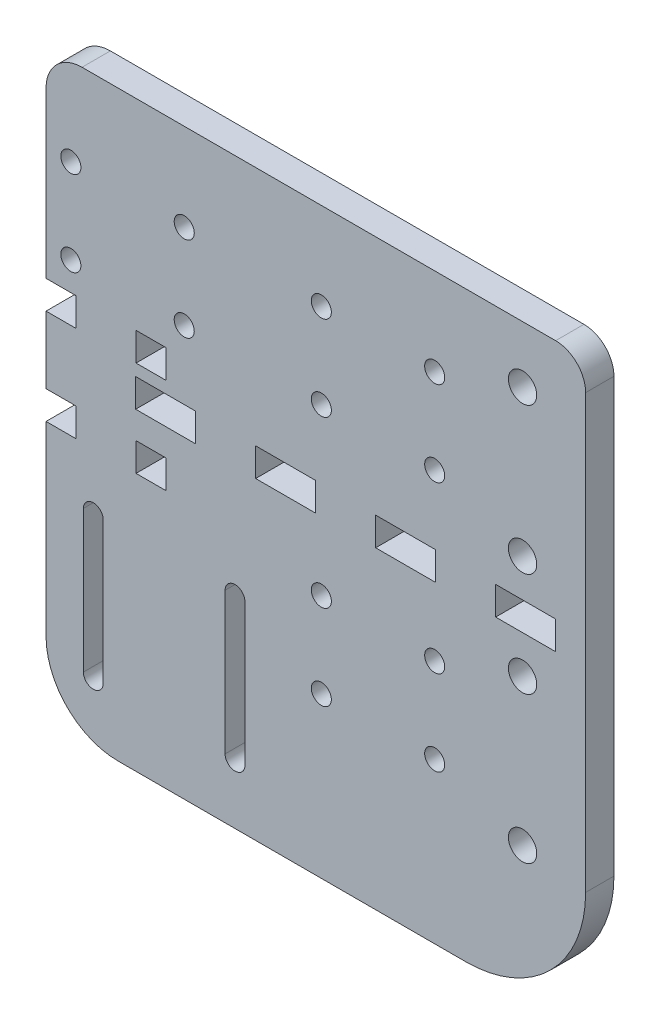
SolidWorks part; units mm, degrees
ref_plane "Front Plane" through (0, 0, 0) normal (0, 0, 1) x (1, 0, 0)
ref_plane "Top Plane" through (0, 0, 0) normal (0, 1, 0) x (1, 0, 0)
ref_plane "Right Plane" through (0, 0, 0) normal (1, 0, 0) x (0, 0, -1)
sketch "Sketch1" plane through (0, 0, 0) normal (0, 0, 1) x (-1, 0, 0)
  line L0 (72.0987, 7.3834) -> (72.0987, -6.8406)
  line L1 (32.0987, 55.3834) -> (32.0987, 25.3834) construction
  line L2 (46.6987, 13.3834) -> (53.0487, 13.3834)
  line L4 (46.6987, 13.3834) -> (46.6987, 7.3834)
  line L5 (46.6987, 7.3834) -> (53.0487, 7.3834)
  line L7 (72.0987, -42.8406) -> (72.0987, -12.8406)
  line L8 (-15.4204, 10.1785) -> (-15.4204, -12.8406)
  line L9 (-35.7704, 4.6785) -> (-35.7704, 45.6785) construction
  line L10 (-35.7704, 45.6785) -> (-21.7704, 45.6785) construction
  line L11 (-21.7704, 45.6785) -> (-21.7704, 4.6785) construction
  line L12 (-21.7704, 4.6785) -> (-35.7704, 4.6785) construction
  line L13 (-1015.4204, -1.3311) -> (48984.5796, -1.3311) construction
  line L14 (-15.4204, 25.1785) -> (-21.7704, 25.1785)
  line L15 (-21.7704, -7.3406) -> (-35.7704, -7.3406) construction
  line L16 (-21.7704, -48.3406) -> (-21.7704, -7.3406) construction
  line L17 (-35.7704, -48.3406) -> (-21.7704, -48.3406) construction
  line L18 (-35.7704, -7.3406) -> (-35.7704, -48.3406) construction
  line L19 (34.1987, 55.3834) -> (34.1987, 25.3834)
  line L20 (29.9987, 55.3834) -> (29.9987, 25.3834)
  line L21 (62.0987, 55.3834) -> (62.0987, 25.3834) construction
  line L22 (-15.4204, 40.1785) -> (-15.4204, 10.1785)
  line L23 (72.0987, -42.8406) -> (72.0987, -47.7342)
  line L24 (64.4787, -55.3542) -> (51.6526, -55.3542)
  line L25 (53.0487, 13.3834) -> (53.0487, 7.3834)
  line L26 (73.3068, 13.3834) -> (74.536, 13.3834) construction
  line L27 (65.7487, 13.3834) -> (72.0987, 13.3834)
  line L28 (65.7487, 13.3834) -> (65.7487, 7.3834)
  line L29 (65.7487, 7.3834) -> (72.0987, 7.3834)
  line L30 (64.1987, 55.3834) -> (64.1987, 25.3834)
  line L31 (46.6987, -6.8406) -> (53.0487, -6.8406)
  line L32 (72.0987, 13.3834) -> (72.0987, 52.7789)
  line L33 (46.6987, -6.8406) -> (46.6987, -12.8406)
  line L34 (59.9987, 55.3834) -> (59.9987, 25.3834)
  line L35 (24.3526, 50.6689) -> (24.3526, 20.6689) construction
  line L42 (46.6987, -12.8406) -> (53.0487, -12.8406)
  line L43 (53.0487, -6.8406) -> (53.0487, -12.8406)
  line L44 (-35.7704, -4.3283) -> (-35.7704, 1.6661)
  line L45 (-35.7704, 1.6661) -> (-23.0704, 1.6661)
  line L46 (-23.0704, 1.6661) -> (-23.0704, -4.3283)
  line L47 (65.7487, -6.8406) -> (72.0987, -6.8406)
  line L48 (-10.3704, -4.3283) -> (-10.3704, 1.6661)
  line L49 (65.7487, -6.8406) -> (65.7487, -12.8406)
  line L50 (65.7487, -12.8406) -> (72.0987, -12.8406)
  line L51 (26.2526, -55.3542) -> (-35.7704, -55.3542)
  line L52 (-42.1204, 42.6189) -> (-42.1204, -49.0042)
  line L53 (-10.3704, 1.6661) -> (2.3296, 1.6661)
  line L54 (2.3296, 1.6661) -> (2.3296, -4.3283)
  line L55 (56.8587, 68.0189) -> (-16.7204, 68.0189)
  line L56 (15.0296, -4.3283) -> (15.0296, 1.6661)
  line L57 (15.0296, 1.6661) -> (27.7296, 1.6661)
  line L58 (27.7296, 1.6661) -> (27.7296, -4.3283)
  line L60 (40.4296, -4.3283) -> (40.4296, 1.6661)
  line L61 (40.4296, 1.6661) -> (53.1296, 1.6661)
  line L62 (53.1296, 1.6661) -> (53.1296, -4.3283)
  line L67 (40.4296, -4.3283) -> (53.1296, -4.3283)
  line L68 (15.0296, -4.3283) -> (27.7296, -4.3283)
  line L69 (-10.3704, -4.3283) -> (2.3296, -4.3283)
  line L70 (-35.7704, -4.3283) -> (-23.0704, -4.3283)
  line L75 (26.2526, -55.3542) -> (45.3026, -55.3542)
  line L94 (51.6526, -55.3542) -> (45.3026, -55.3542)
  line L95 (45.3026, -55.3542) -> (45.4172, -55.5387)
  circle A0 centre (-10.1704, -18.8406) radius 2.125
  circle A1 centre (13.8296, -18.8406) radius 2.125
  circle A2 centre (13.8296, -36.8406) radius 2.125
  circle A3 centre (-10.1704, -36.8406) radius 2.125
  circle A4 centre (-28.7704, -43.3406) radius 3
  circle A5 centre (-28.7704, -12.3406) radius 3
  circle A6 centre (42.8487, -18.8406) radius 2.125
  circle A7 centre (66.8487, -18.8406) radius 2.125
  circle A8 centre (-28.7704, 9.6785) radius 3
  circle A9 centre (-28.7704, 40.6785) radius 3
  circle A10 centre (66.8487, -36.8406) radius 2.125
  circle A11 centre (42.8487, -36.8406) radius 2.125
  arc A12 (34.1987, 55.3834) -> (29.9987, 55.3834) centre (32.0987, 55.3834) ccw
  arc A13 (29.9987, 25.3834) -> (34.1987, 25.3834) centre (32.0987, 25.3834) ccw
  arc A14 (64.1987, 55.3834) -> (59.9987, 55.3834) centre (62.0987, 55.3834) ccw
  arc A15 (59.9987, 25.3834) -> (64.1987, 25.3834) centre (62.0987, 25.3834) ccw
  arc A16 (72.0987, 52.7789) -> (56.8587, 68.0189) centre (56.8587, 52.7789) ccw
  arc A17 (-16.7204, 68.0189) -> (-42.1204, 42.6189) centre (-16.7204, 42.6189) ccw
  arc A18 (64.4787, -55.3542) -> (72.0987, -47.7342) centre (64.4787, -47.7342) ccw
  arc A19 (-35.7704, -55.3542) -> (-42.1204, -49.0042) centre (-35.7704, -49.0042) cw
  circle A20 centre (-10.1704, 34.1785) radius 2.125
  circle A21 centre (13.8296, 34.1785) radius 2.125
  circle A22 centre (-10.1704, 16.1785) radius 2.125
  circle A23 centre (13.8296, 16.1785) radius 2.125
  point P54 (32.0987, 40.3834)
  point P62 (62.0987, 40.3834)
  point P142 (-15.4204, -1.3311)
  dimension "D9" = 25.4
  dimension "D11" = 6.35
  dimension "D2" = 15.24
  dimension "D3" = 7.62
  dimension "D6" = 30
  dimension "D12" = 4
extrude "Boss-Extrude1" add sketch "Sketch1" along normal blind 5.9944
